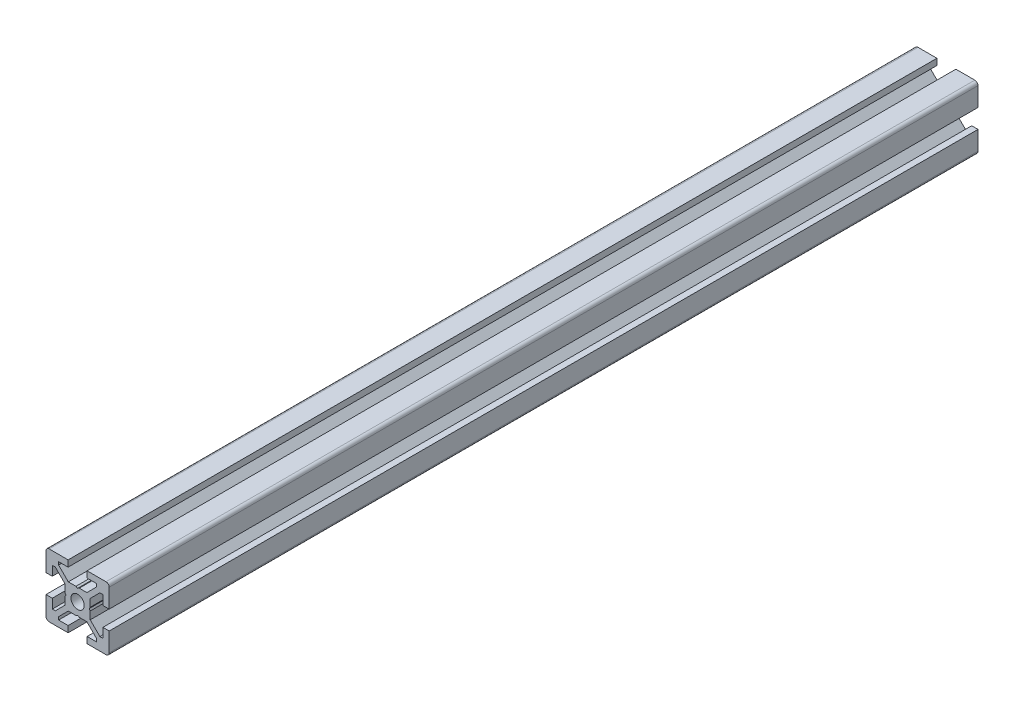
SolidWorks part; units mm, degrees
material "2014 合金"
ref_plane "正面" through (0, 0, 0) normal (0, 0, 1) x (1, 0, 0)
ref_plane "平面" through (0, 0, 0) normal (0, 1, 0) x (1, 0, 0)
ref_plane "右側面" through (0, 0, 0) normal (1, 0, 0) x (0, 0, -1)
ref_plane "平面1" through (0, 0, 0) normal (0, 0, 1) x (1, 0, 0)
sketch "ｽｹｯﾁ1" plane through (0, 0, 0) normal (0, 0, 1) x (1, 0, 0)
  line L0 (-10, -3) -> (-10, -9)
  line L1 (-9, -10) -> (-3, -10)
  line L2 (-3, -10) -> (-3, -8)
  line L3 (-3, -8) -> (-6, -8)
  line L4 (-6, -8) -> (-6, -7.0607)
  line L5 (-6, -7.0607) -> (-2.9393, -4)
  line L6 (-2.9393, -4) -> (-0.5196, -4)
  line L7 (-0.5196, -4) -> (0, -3.7)
  line L8 (0, -3.7) -> (0.5196, -4)
  line L9 (0.5196, -4) -> (2.9393, -4)
  line L10 (2.9393, -4) -> (6, -7.0607)
  line L11 (6, -7.0607) -> (6, -8)
  line L12 (6, -8) -> (3, -8)
  line L13 (3, -8) -> (3, -10)
  line L14 (3, -10) -> (9, -10)
  line L15 (10, -9) -> (10, -3)
  line L16 (10, -3) -> (8, -3)
  line L17 (8, -3) -> (8, -6)
  line L18 (8, -6) -> (7.0607, -6)
  line L19 (7.0607, -6) -> (4, -2.9393)
  line L20 (4, -2.9393) -> (4, -0.5196)
  line L21 (4, -0.5196) -> (3.7, 0)
  line L22 (3.7, 0) -> (4, 0.5196)
  line L23 (4, 0.5196) -> (4, 2.9393)
  line L24 (4, 2.9393) -> (7.0607, 6)
  line L25 (7.0607, 6) -> (8, 6)
  line L26 (8, 6) -> (8, 3)
  line L27 (8, 3) -> (10, 3)
  line L28 (10, 3) -> (10, 9)
  line L29 (9, 10) -> (3, 10)
  line L30 (3, 10) -> (3, 8)
  line L31 (3, 8) -> (6, 8)
  line L32 (6, 8) -> (6, 7.0607)
  line L33 (6, 7.0607) -> (2.9393, 4)
  line L34 (2.9393, 4) -> (0.5196, 4)
  line L35 (0.5196, 4) -> (0, 3.7)
  line L36 (0, 3.7) -> (-0.5196, 4)
  line L37 (-0.5196, 4) -> (-2.9393, 4)
  line L38 (-2.9393, 4) -> (-6, 7.0607)
  line L39 (-6, 7.0607) -> (-6, 8)
  line L40 (-6, 8) -> (-3, 8)
  line L41 (-3, 8) -> (-3, 10)
  line L42 (-3, 10) -> (-9, 10)
  line L43 (-10, 9) -> (-10, 3)
  line L44 (-10, 3) -> (-8, 3)
  line L45 (-8, 3) -> (-8, 6)
  line L46 (-8, 6) -> (-7.0607, 6)
  line L47 (-7.0607, 6) -> (-4, 2.9393)
  line L48 (-4, 2.9393) -> (-4, 0.5196)
  line L49 (-4, 0.5196) -> (-3.7, 0)
  line L50 (-3.7, 0) -> (-4, -0.5196)
  line L51 (-4, -0.5196) -> (-4, -2.9393)
  line L52 (-4, -2.9393) -> (-7.0607, -6)
  line L53 (-7.0607, -6) -> (-8, -6)
  line L54 (-8, -6) -> (-8, -3)
  line L55 (-8, -3) -> (-10, -3)
  arc A0 (-10, -9) -> (-9, -10) centre (-9, -9) ccw
  arc A1 (9, -10) -> (10, -9) centre (9, -9) ccw
  arc A2 (10, 9) -> (9, 10) centre (9, 9) ccw
  arc A3 (-9, 10) -> (-10, 9) centre (-9, 9) ccw
extrude "ﾎﾞｽ - 押し出し1" add sketch "ｽｹｯﾁ1" against normal blind 275
ref_plane "平面2" through (0, 0, 0) normal (1, 0, 0) x (0, 0, -1)
sketch "ｽｹｯﾁ2" plane through (0, 0, 0) normal (1, 0, 0) x (0, 0, -1)
  line L0 (0, 0) -> (0, 2.1)
  line L1 (0, 2.1) -> (260, 2.1)
  line L2 (260, 2.1) -> (260, 0)
  line L3 (260, 0) -> (0, 0)
  line L4 (260, 0) -> (0, 0) construction
revolve "ｶｯﾄ - 回転1" cut sketch "ｽｹｯﾁ2" angle 360 about L4
